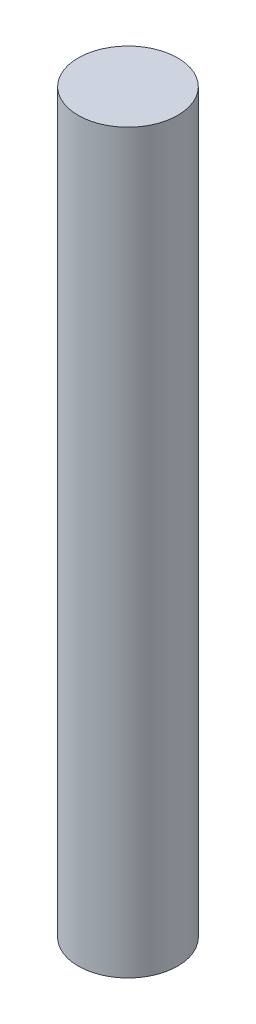
SolidWorks part; units mm, degrees
ref_plane "Piano frontale" through (0, 0, 0) normal (0, 0, 1) x (1, 0, 0)
ref_plane "Piano superiore" through (0, 0, 0) normal (0, 1, 0) x (1, 0, 0)
ref_plane "Piano destro" through (0, 0, 0) normal (1, 0, 0) x (0, 0, -1)
sketch "Schizzo1" plane through (0, 0, 0) normal (0, 1, 0) x (1, 0, 0)
  circle A0 centre (0, 0) radius 8
  dimension "D1" = 16
extrude "Estrusione-Estrusione1" add sketch "Schizzo1" along normal blind 118.46
